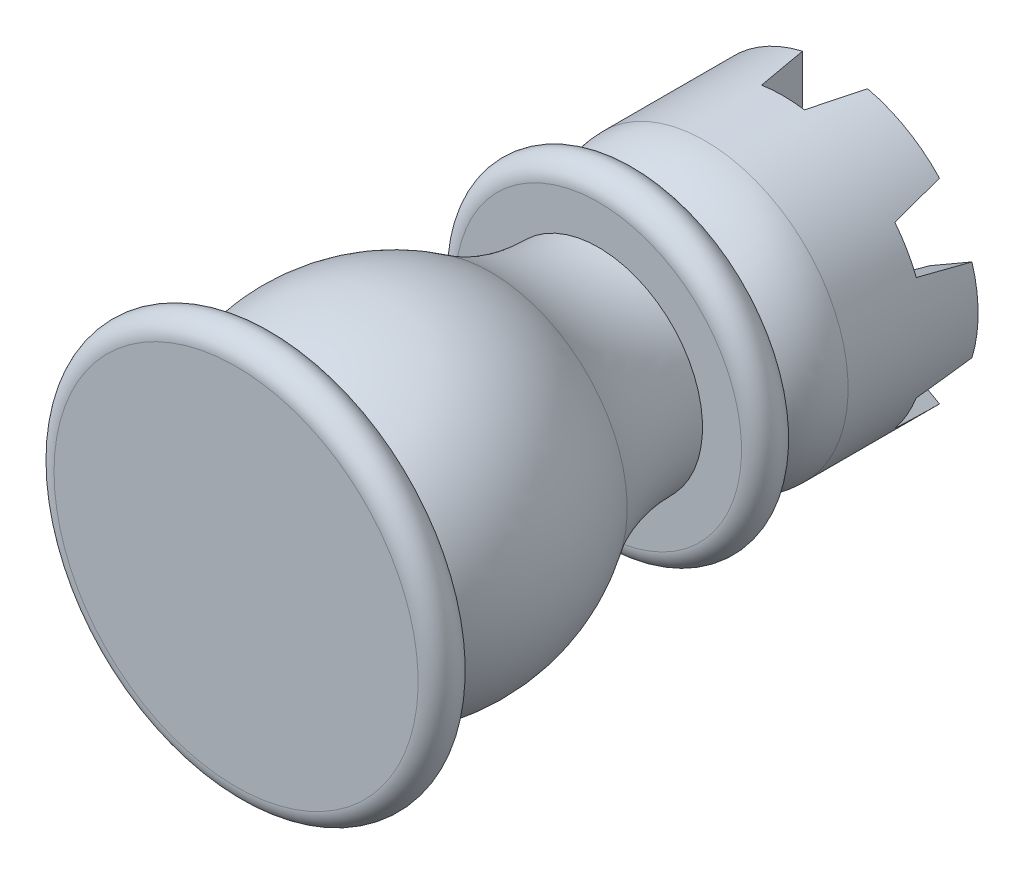
SolidWorks part; units mm, degrees
ref_plane "Front Plane" through (0, 0, 0) normal (0, 0, 1) x (1, 0, 0)
ref_plane "Top Plane" through (0, 0, 0) normal (0, 1, 0) x (1, 0, 0)
ref_plane "Right Plane" through (0, 0, 0) normal (1, 0, 0) x (0, 0, -1)
sketch "Sketch1" plane through (0, 0, 0) normal (0, 1, 0) x (1, 0, 0)
  line L0 (-14, 0) -> (14, 0) construction
  line L1 (-14, 1.5) -> (14, 1.5)
  line L2 (-14, -1.5) -> (14, -1.5)
  line L3 (0, 0) -> (0, 1.5) construction
  line L4 (0, 1.5) -> (0, 27.5708) construction
  line L5 (-13, 9.7916) -> (-13, 15.1582) construction
  line L6 (-10.5, 1.5) -> (10.5, 1.5)
  line L7 (-8, 26.3747) -> (8, 26.3747)
  line L8 (13, 9.7916) -> (13, 15.1582) construction
  line L9 (0, 26.3747) -> (0, 27.8747) construction
  line L10 (-11, 27.8747) -> (11, 27.8747) construction
  line L11 (-11, 29.3747) -> (11, 29.3747)
  line L12 (-11, 26.3747) -> (11, 26.3747)
  line L13 (-8, 29.3747) -> (8, 29.3747)
  line L14 (0, 36.5708) -> (0, 26.3747)
  line L15 (-11, 36.5708) -> (11, 36.5708)
  line L16 (-11, 36.5708) -> (-11, 34.5708)
  line L17 (11, 34.5708) -> (11, 36.5708)
  line L18 (10.5, 1.5) -> (-10.5, 1.5)
  line L19 (0, 26.3747) -> (0, 29.3747) construction
  line L20 (0, 1.5) -> (0, 0)
  line L21 (-8, 26.3747) -> (-8, 20.0327) construction
  line L22 (0, 26.3747) -> (0, -1.5)
  arc A0 (-14, 1.5) -> (-14, -1.5) centre (-14, 0) ccw
  arc A1 (14, -1.5) -> (14, 1.5) centre (14, 0) ccw
  arc A4 (-12.5, 15.6625) -> (-8, 26.3747) centre (-23, 26.3747) ccw
  arc A5 (12.5, 15.6625) -> (8, 26.3747) centre (23, 26.3747) cw
  arc A6 (-11, 29.3747) -> (-11, 26.3747) centre (-11, 27.8747) ccw
  arc A7 (11, 26.3747) -> (11, 29.3747) centre (11, 27.8747) ccw
  arc A10 (11, 34.5708) -> (8, 29.3747) centre (5, 34.5708) cw
  arc A11 (-11, 34.5708) -> (-8, 29.3747) centre (-5, 34.5708) ccw
  arc A12 (11.8742, -1.5) -> (-7.8742, -1.5) centre (2, 9.7916) ccw
  arc A13 (-11.8742, -1.5) -> (7.8742, -1.5) centre (-2, 9.7916) cw
  point P2 (0, 0)
  point P31 (0, 27.8747)
  dimension "D1" = 1.5
  dimension "D2" = 26
  dimension "D3" = 21
  dimension "D5" = 21
  dimension "D6" = 30
  dimension "D9" = 1.5
  dimension "D11" = 2
  dimension "D14" = 6
  dimension "D15" = 30
  dimension "D4" = 28
  dimension "D7" = 16
  dimension "D8" = 1.5
  dimension "D10" = 22
  dimension "D12" = 16
  dimension "D13" = 22
revolve "Revolve2" add sketch "Sketch1" angle 360 about L14
sketch "Sketch5" plane through (0, 0, -36.5708) normal (0, 0, -1) x (-1, 0, 0)
  line L0 (0, 0) -> (0, 11) construction
  circle A1 centre (0, 0) radius 11
  circle A2 centre (0, 0) radius 11
  dimension "D1" = 0
extrude "Boss-Extrude1" add sketch "Sketch5" along normal blind 8 contours A2
sketch "Sketch6" plane through (0, 0, 0) normal (0, 1, 0) x (1, 0, 0)
  line L0 (-2.5, 44.5708) -> (2.5, 44.5708)
  line L5 (0, 44.5708) -> (0, 46.1268) construction
  line L6 (-1.6498, 40.5708) -> (1.6498, 40.5708)
  line L7 (-1.6498, 40.5708) -> (-2.5, 44.5708)
  line L8 (1.6498, 40.5708) -> (2.5, 44.5708)
  line L9 (-11, 34.5708) -> (11, 34.5708) construction
  dimension "D1" = 4
  dimension "D2" = 24
  dimension "D3" = 5
  dimension "D4" = 6
extrude "Cut-Extrude1" cut sketch "Sketch6" against normal through all both and the other way through all
pattern_circular "CirPattern1" count 3 over 360 about axis through (0, 0, 0) along (0, 0, 1) of "Cut-Extrude1"
sketch "Sketch7" plane through (0, 0, 0) normal (0, 1, 0) x (1, 0, 0)
  line L0 (0, 36.5708) -> (6, 36.5708)
  line L1 (0, 40.5708) -> (0, 39.4362) construction
  line L2 (1.6498, 40.5708) -> (-1.6498, 40.5708) construction
  line L3 (11, 34.5708) -> (-11, 34.5708) construction
  line L4 (6, 36.5708) -> (9.5498, 56.7029)
  line L6 (0, 56.7029) -> (9.5498, 56.7029)
  line L7 (0, 36.5708) -> (0, 56.7029)
  point P13 (0, 56.4633)
  point P14 (0, 56.9715)
  dimension "D2" = 2
  dimension "D3" = 10
revolve "Cut-Revolve1" cut sketch "Sketch7" angle 360 about L1
